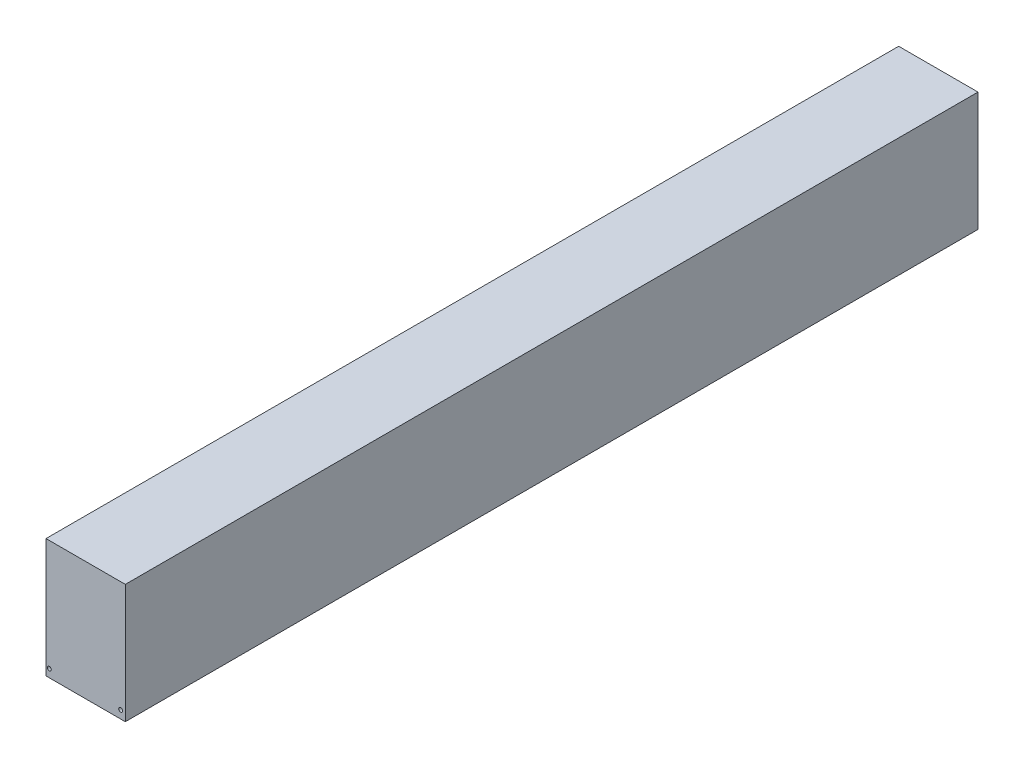
SolidWorks part; units mm, degrees
ref_plane "Front Plane" through (0, 0, 0) normal (0, 0, 1) x (1, 0, 0)
ref_plane "Top Plane" through (0, 0, 0) normal (0, 1, 0) x (1, 0, 0)
ref_plane "Right Plane" through (0, 0, 0) normal (1, 0, 0) x (0, 0, -1)
sketch "Sketch1" plane through (0, 0, 0) normal (0, 0, 1) x (1, 0, 0)
  line L1 (-50, -75) -> (50, -75)
  line L2 (-50, -75) -> (-50, 75)
  line L3 (-50, 75) -> (50, 75)
  line L4 (50, -75) -> (50, 75)
  line L5 (-50, -75) -> (50, 75) construction
  line L6 (-50, 75) -> (50, -75) construction
  point P0 (0, 0)
  dimension "D1" = 100
  dimension "D2" = 150
extrude "Boss-Extrude1" add sketch "Sketch1" along normal blind 1075
sketch "Sketch3" plane through (0, -75, 0) normal (0, -1, 0) x (1, 0, 0)
  line L0 (45.75, 1068.75) -> (50, 1068.75) construction
  line L1 (50, 1075) -> (50, 0) construction
  line L2 (45.75, 1068.75) -> (45.75, 1075) construction
  line L3 (-50, 1075) -> (50, 1075) construction
  circle A0 centre (45.75, 1068.75) radius 1.7
  dimension "D1" = 3.4
  dimension "D2" = 4.25
  dimension "D3" = 6.25
extrude "Cut-Extrude1" cut sketch "Sketch3" against normal blind 3.5
pattern_linear "LPattern1" count 29 spacing 37.95 along (0, 0, -1) of "Cut-Extrude1"
pattern_linear "LPattern2" count 4 spacing 30.425 along (-1, 0, 0) of "Cut-Extrude1"
ref_plane "Plane6" through (0, 0, 0) normal (-1, 0, 0) x (0, 0, 1)
mirror "Mirror1" about plane through (0, 0, 0) normal (-1, 0, 0) of "LPattern1", "Cut-Extrude1"
ref_plane "Plane7" through (0, 0, 537.5) normal (0, 0, -1) x (-1, 0, 0)
mirror "Mirror2" about plane through (0, 0, 537.5) normal (0, 0, -1) of "LPattern2", "Cut-Extrude1"
sketch "Sketch4" plane through (0, 0, 0) normal (0, 0, -1) x (-1, 0, 0)
  circle A0 centre (-44.15, -65) radius 2.5
  circle A1 centre (45.85, -65) radius 2.5
extrude "Cut-Extrude2" cut sketch "Sketch4" against normal blind 7.5
mirror "Mirror3" about plane through (0, 0, 537.5) normal (0, 0, -1) of "Cut-Extrude2"
